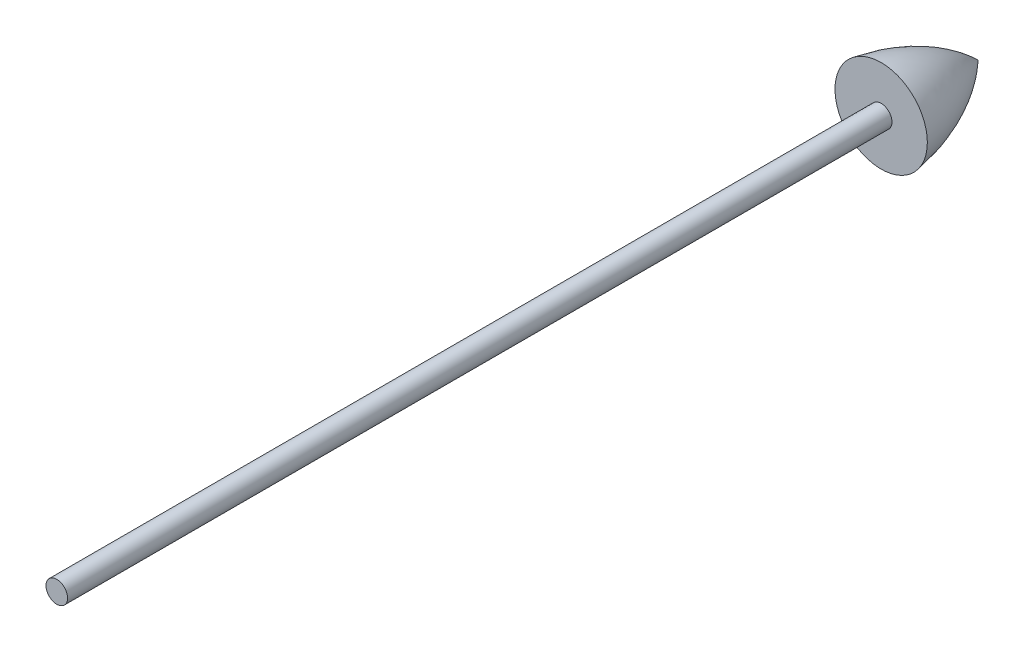
SolidWorks part; units mm, degrees
ref_plane "Front Plane" through (0, 0, 0) normal (0, 0, 1) x (1, 0, 0)
ref_plane "Top Plane" through (0, 0, 0) normal (0, 1, 0) x (1, 0, 0)
ref_plane "Right Plane" through (0, 0, 0) normal (1, 0, 0) x (0, 0, -1)
sketch "Sketch1" plane through (0, 0, 0) normal (1, 0, 0) x (0, 0, -1)
  line L0 (358.4801, 887.2194) -> (1791.1468, 887.2194) construction
sketch "Sketch2" plane through (0, 0, 0) normal (1, 0, 0) x (0, 0, -1)
  line L0 (0, 0) -> (5000, 33.3333)
  dimension "D1" = 5000
sketch "Sketch4" plane through (0, 0, 0) normal (1, 0, 0) x (0, 0, -1)
  line L1 (1228.2901, 297.3225) -> (1962.3176, 297.3225)
  line L2 (1962.3176, 297.3225) -> (3617.1486, 297.3225)
  line L3 (3617.1486, 297.3225) -> (3633.2454, 297.3225)
  line L4 (3633.2454, 297.3225) -> (3633.2454, 411.4997)
  line L5 (1228.2901, 297.3225) -> (1158.9317, 297.3225)
  line L7 (1158.9317, 262.4372) -> (3945.843, 262.4372)
  line L10 (1158.9317, 297.3225) -> (971.847, 297.3225)
  line L11 (971.847, 297.3225) -> (971.847, 262.4372)
  line L12 (971.847, 262.4372) -> (1158.9317, 262.4372)
  spline S0 degree 2 poles (3633.2454, 411.4997) (3821.7406, 382.0928) (3945.843, 262.4372) knots 0 0 0 0.92051 0.92051 0.92051
revolve "Revolve4" add sketch "Sketch4" angle 360 about L7
